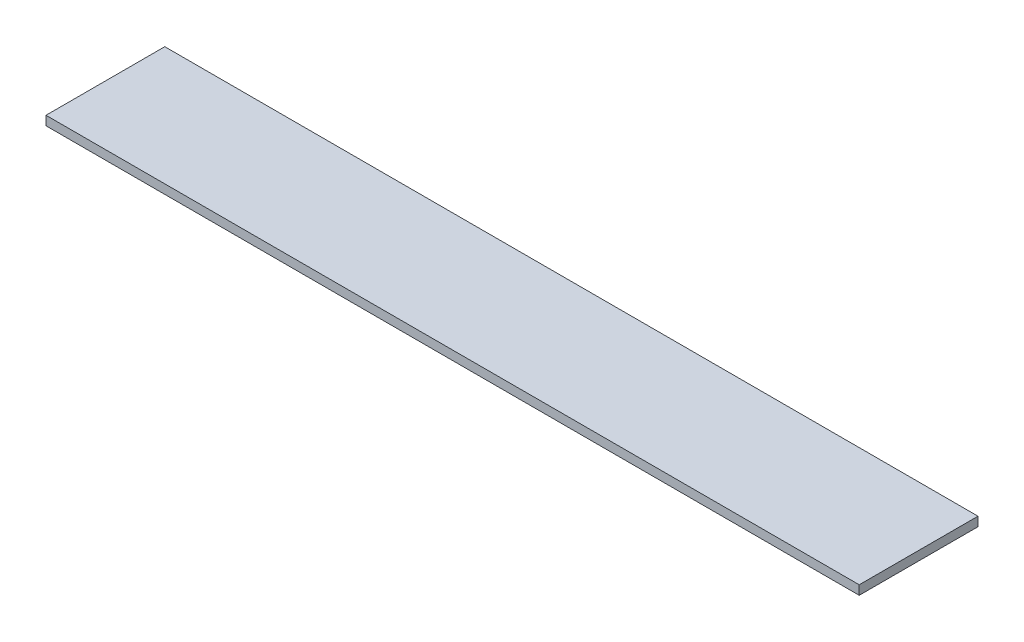
SolidWorks part; units mm, degrees
ref_plane "Alzado" through (0, 0, 0) normal (0, 0, 1) x (1, 0, 0)
ref_plane "Planta" through (0, 0, 0) normal (0, 1, 0) x (1, 0, 0)
ref_plane "Vista lateral" through (0, 0, 0) normal (1, 0, 0) x (0, 0, -1)
sketch "Croquis1" plane through (0, 0, 0) normal (0, 1, 0) x (1, 0, 0)
  line L1 (0, 0) -> (890, 0)
  line L2 (0, 0) -> (0, 130)
  line L3 (0, 130) -> (890, 130)
  line L4 (890, 0) -> (890, 130)
  dimension "D1" = 890
  dimension "D2" = 130
extrude "Saliente-Extruir1" add sketch "Croquis1" along normal blind 10
